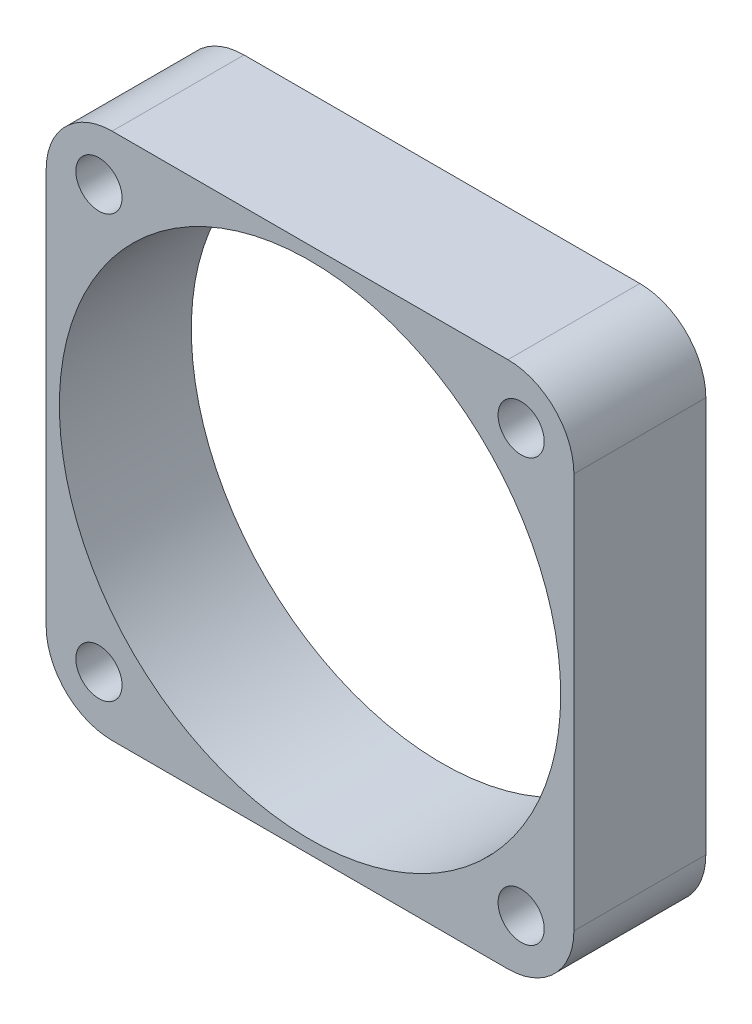
SolidWorks part; units mm, degrees
material "ABS PC"
ref_plane "Front Plane" through (0, 0, 0) normal (0, 0, 1) x (1, 0, 0)
ref_plane "Top Plane" through (0, 0, 0) normal (0, 1, 0) x (1, 0, 0)
ref_plane "Right Plane" through (0, 0, 0) normal (1, 0, 0) x (0, 0, -1)
sketch "Sketch1" plane through (0, 0, 0) normal (0, 0, 1) x (1, 0, 0)
  line L1 (0, 0) -> (40, 0)
  line L2 (0, 0) -> (0, 40)
  line L3 (0, 40) -> (40, 40)
  line L4 (40, 0) -> (40, 40)
  dimension "D1" = 40
extrude "Boss-Extrude1" add sketch "Sketch1" along normal blind 10
sketch "Sketch3" plane through (0, 0, 10) normal (0, 0, 1) x (1, 0, 0)
  line L0 (0, 20) -> (20, 20) construction
  line L1 (0, 40) -> (0, 0) construction
  line L2 (20, 20) -> (20, 0) construction
  line L3 (0, 0) -> (40, 0) construction
  line L4 (4, 36) -> (36, 4) construction
  circle A0 centre (20, 20) radius 19
  circle A1 centre (4, 36) radius 1.75
  circle A2 centre (36, 36) radius 1.75
  circle A3 centre (36, 4) radius 1.75
  circle A4 centre (4, 4) radius 1.75
  dimension "D1" = 38
  dimension "D6" = 3.5
  dimension "D2" = 32
  dimension "D3" = 45
extrude "Cut-Extrude1" cut sketch "Sketch3" against normal blind 10 contours A0 | A1 | A4 | A3 | A2
fillet "Fillet1" radius 5 4 edges at (0, 0, 5) (40, 0, 5) (0, 40, 5) (40, 40, 5)
